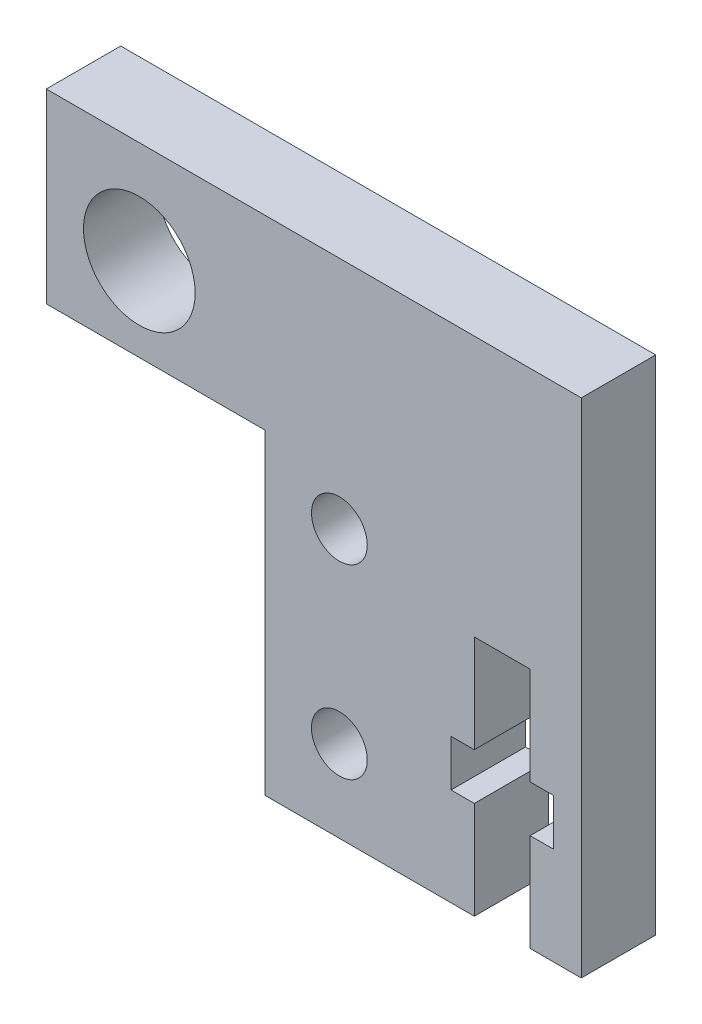
SolidWorks part; units mm, degrees
ref_plane "Спереди" through (0, 0, 0) normal (0, 0, 1) x (1, 0, 0)
ref_plane "Сверху" through (0, 0, 0) normal (0, 1, 0) x (1, 0, 0)
ref_plane "Справа" through (0, 0, 0) normal (1, 0, 0) x (0, 0, -1)
sketch "Эскиз1" plane through (0, 0, 0) normal (0, 0, 1) x (1, 0, 0)
  line L0 (0, 9.4) -> (17, 9.4) construction
  line L1 (0, 0) -> (17, 0)
  line L2 (0, 0) -> (0, 27)
  line L3 (0, 27) -> (17, 27)
  line L4 (17, 0) -> (17, 27)
  circle A0 centre (4, 14.4) radius 1.5
  circle A3 centre (4, 4.4) radius 1.5
  point P13 (0, 27)
  point P14 (0, 27)
  dimension "D3" = 3
  dimension "D4" = 12.6
  dimension "D5" = 4
  dimension "D6" = 5
  dimension "D8" = 4.4
  dimension "D1" = 17
  dimension "D2" = 27
extrude "Бобышка-Вытянуть1" add sketch "Эскиз1" along normal blind 4
sketch "Эскиз2" plane through (0, 0, 4) normal (0, 0, 1) x (1, 0, 0)
  line L0 (11.25, 0) -> (11.25, 5.25)
  line L1 (0, 0) -> (17, 0) construction
  line L2 (11.25, 5.25) -> (10, 5.25)
  line L3 (10, 5.25) -> (10, 7.75)
  line L4 (10, 7.75) -> (11.25, 7.75)
  line L5 (11.25, 7.75) -> (11.25, 13)
  line L6 (11.25, 13) -> (14.25, 13)
  line L7 (12.75, 13) -> (12.75, 0) construction
  line L8 (14.25, 0) -> (14.25, 5.25)
  line L9 (14.25, 5.25) -> (15.5, 5.25)
  line L10 (15.5, 5.25) -> (15.5, 7.75)
  line L11 (15.5, 7.75) -> (14.25, 7.75)
  line L12 (14.25, 7.75) -> (14.25, 13)
  line L13 (17, 0) -> (17, 27) construction
  dimension "D1" = 13
  dimension "D2" = 2.5
  dimension "D3" = 3
  dimension "D4" = 5.5
  dimension "D5" = 1.5
extrude "Вырез-Вытянуть1" cut sketch "Эскиз2" against normal blind 4 and the other way through all
sketch "Эскиз5" plane through (0, 0, 4) normal (0, 0, 1) x (1, 0, 0)
  line L1 (0, 27) -> (-11.75, 27)
  line L2 (0, 27) -> (0, 17)
  line L3 (0, 17) -> (-11.75, 17)
  line L4 (-11.75, 27) -> (-11.75, 17)
  line L5 (17, 27) -> (0, 27) construction
  line L6 (0, 27) -> (0, 0) construction
  circle A1 centre (-6.75, 21.5) radius 3
  dimension "D3" = 6
  dimension "D4" = 5.5
  dimension "D5" = 5
  dimension "D1" = 10
  dimension "D2" = 11.75
extrude "Бобышка-Вытянуть2" add sketch "Эскиз5" against normal blind 4
